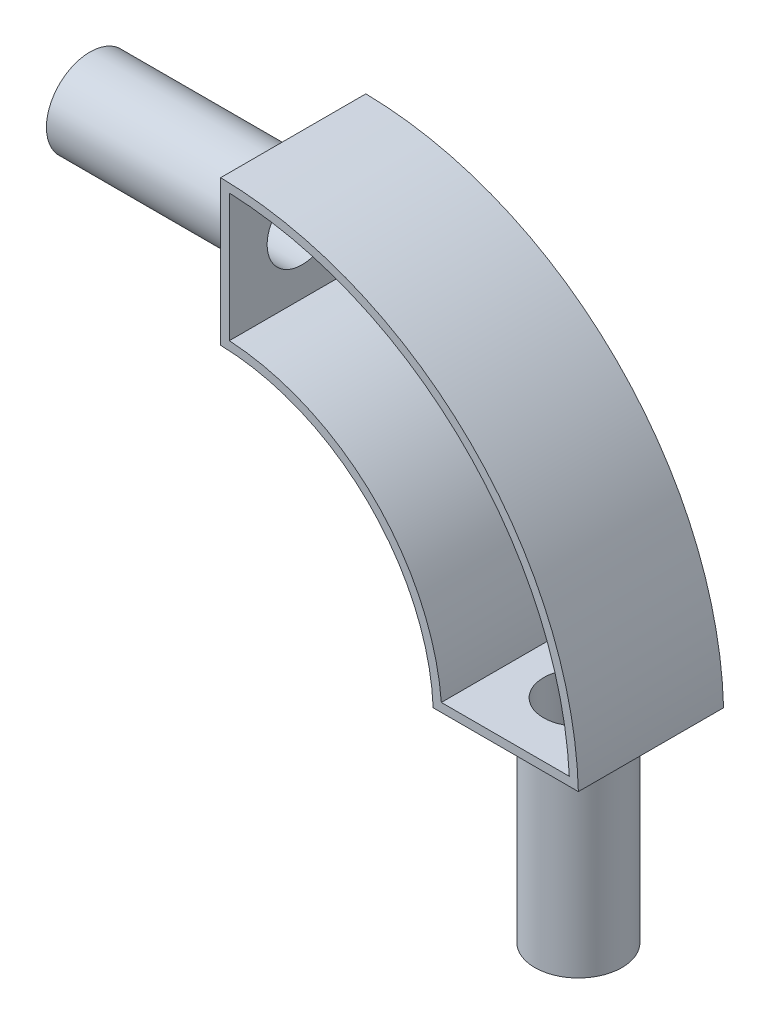
SolidWorks part; units mm, degrees
ref_plane "Front Plane" through (0, 0, 0) normal (0, 0, 1) x (1, 0, 0)
ref_plane "Top Plane" through (0, 0, 0) normal (0, 1, 0) x (1, 0, 0)
ref_plane "Right Plane" through (0, 0, 0) normal (1, 0, 0) x (0, 0, -1)
sketch "Sketch1" plane through (0, 0, 0) normal (0, 0, 1) x (1, 0, 0)
  line L0 (0, 153.4006) -> (0, -161.993) construction
  line L1 (-287.5945, 0) -> (261.8171, 0) construction
  line L2 (0, 71.5125) -> (0, 121.5125)
  line L3 (73.1929, 0) -> (123.1929, 0)
  arc A0 (0, 121.5125) -> (123.1929, 0) centre (-1.7588, -3.4751) cw
  arc A1 (0, 71.5125) -> (73.1929, 0) centre (-1.7269, -3.4676) cw
  dimension "D1" = 125
  dimension "D2" = 75
  dimension "D3" = 50
  dimension "D4" = 50
extrude "Boss-Extrude1" add sketch "Sketch1" along normal mid plane 50
shell "Shell1" thickness 3
sketch "Sketch2" plane through (0, 0, 0) normal (-1, 0, 0) x (0, 0, 1)
  circle A0 centre (0, 96.5125) radius 15
  dimension "D1" = 30
extrude "Boss-Extrude2" add sketch "Sketch2" along normal blind 70 contours A0
sketch "Sketch3" plane through (-70, 0, 0) normal (-1, 0, 0) x (0, 0, 1)
  circle A0 centre (0, 96.5125) radius 12
  dimension "D1" = 24
extrude "Cut-Extrude1" cut sketch "Sketch3" against normal blind 75 contours A0
sketch "Sketch4" plane through (0, 0, 0) normal (0, -1, 0) x (1, 0, 0)
  circle A0 centre (98.1929, 0) radius 15
  dimension "D1" = 30
extrude "Boss-Extrude3" add sketch "Sketch4" along normal blind 70 contours A0
sketch "Sketch5" plane through (0, -70, 0) normal (0, -1, 0) x (1, 0, 0)
  circle A0 centre (98.1929, 0) radius 12
  dimension "D1" = 24
extrude "Cut-Extrude2" cut sketch "Sketch5" against normal blind 75 contours A0
